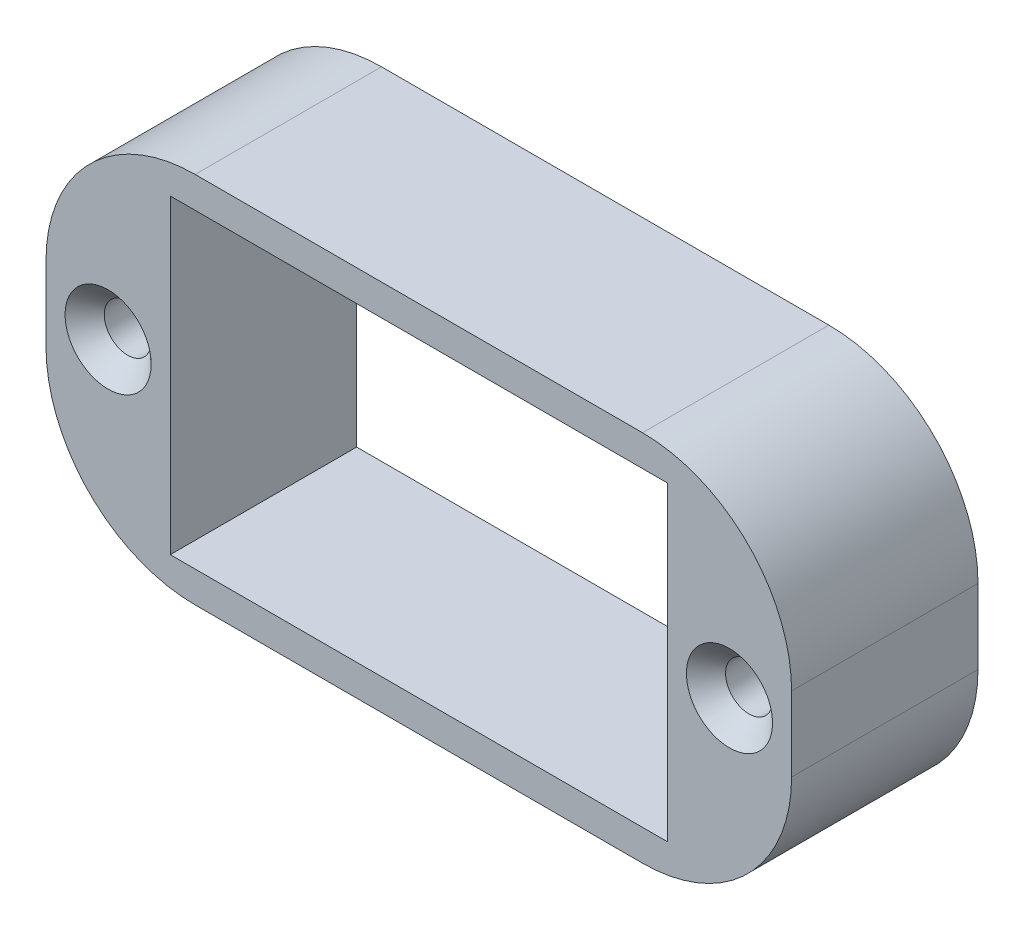
SolidWorks part; units mm, degrees
ref_plane "Front Plane" through (0, 0, 0) normal (0, 0, 1) x (1, 0, 0)
ref_plane "Top Plane" through (0, 0, 0) normal (0, 1, 0) x (1, 0, 0)
ref_plane "Right Plane" through (0, 0, 0) normal (1, 0, 0) x (0, 0, -1)
sketch "Sketch1" plane through (0, 0, 0) normal (0, 0, 1) x (1, 0, 0)
  line L1 (19.05, -9.525) -> (-19.05, -9.525)
  line L2 (19.05, -9.525) -> (19.05, 9.525)
  line L3 (19.05, 9.525) -> (-19.05, 9.525)
  line L4 (-19.05, -9.525) -> (-19.05, 9.525)
  line L5 (19.05, -9.525) -> (-19.05, 9.525) construction
  line L6 (19.05, 9.525) -> (-19.05, -9.525) construction
  point P0 (0, 0)
  dimension "D1" = 38.1
  dimension "D2" = 19.05
extrude "Boss-Extrude1" add sketch "Sketch1" along normal blind 9.525
sketch "Sketch2" plane through (0, 0, 9.525) normal (0, 0, 1) x (1, 0, 0)
  line L1 (12.7, -7.9375) -> (-12.7, -7.9375)
  line L2 (12.7, -7.9375) -> (12.7, 7.9375)
  line L3 (12.7, 7.9375) -> (-12.7, 7.9375)
  line L4 (-12.7, -7.9375) -> (-12.7, 7.9375)
  line L5 (12.7, -7.9375) -> (-12.7, 7.9375) construction
  line L6 (12.7, 7.9375) -> (-12.7, -7.9375) construction
  point P0 (0, 0)
  dimension "D1" = 15.875
  dimension "D2" = 25.4
extrude "Cut-Extrude1" cut sketch "Sketch2" against normal blind 9.525
fillet "Fillet1" radius 7.62 4 edges at (19.05, 9.525, 4.7625) (19.05, -9.525, 4.7625) (-19.05, -9.525, 4.7625) (-19.05, 9.525, 4.7625)
hole_wizard "CSK for M2 Flat Head Machine Screw1" positions "Sketch4" profile "Sketch5" countersink size "M2" standard "ANSI Metric" end condition through all
sketch "Sketch4" plane through (0, 0, 9.525) normal (0, 0, 1) x (1, 0, 0)
  line L0 (0, 0) -> (0, 16.77) construction
  point P0 (-15.875, 0)
  point P7 (15.875, 0)
  dimension "D1" = 15.875
sketch "Sketch5" plane through (-15.875, 0, 9.525) normal (1, 0, 0) x (0, -1, 0)
  line L0 (0, 0) -> (0, 9.525)
  line L1 (0, 9.525) -> (1.2, 9.525)
  line L2 (1.2, 9.525) -> (1.2, 1)
  line L3 (1.2, 1) -> (2.2, 0)
  line L5 (2.2, 0) -> (0, 0)
  line L6 (-1.2, 1) -> (-2.2, 0) construction
  line L11 (0, -6.35) -> (0, 107.95) construction
  dimension "Thru Hole Dia." = 2.4
  dimension "Thru Hole Depth" = 9.525
  dimension "Near C'Sink Dia." = 4.4
  dimension "Near C'Sink Angle" = 90
